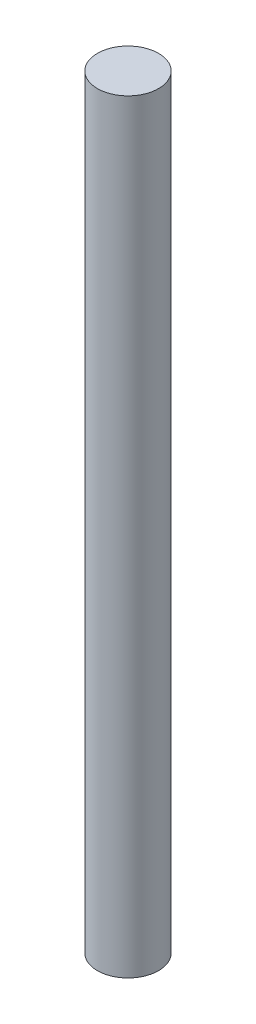
SolidWorks part; units mm, degrees
ref_plane "Alzado" through (0, 0, 0) normal (0, 0, 1) x (1, 0, 0)
ref_plane "Planta" through (0, 0, 0) normal (0, 1, 0) x (1, 0, 0)
ref_plane "Vista lateral" through (0, 0, 0) normal (1, 0, 0) x (0, 0, -1)
sketch "Croquis1" plane through (0, 0, 0) normal (0, 0, 1) x (1, 0, 0)
  line L0 (0, 0) -> (0, 100)
  dimension "D1" = 100
sketch "Croquis2" plane through (0, 0, 0) normal (0, 1, 0) x (1, 0, 0)
  circle A0 centre (0, 0) radius 4
sweep "Barrer1" add profiles "Croquis2" path "Croquis1"
